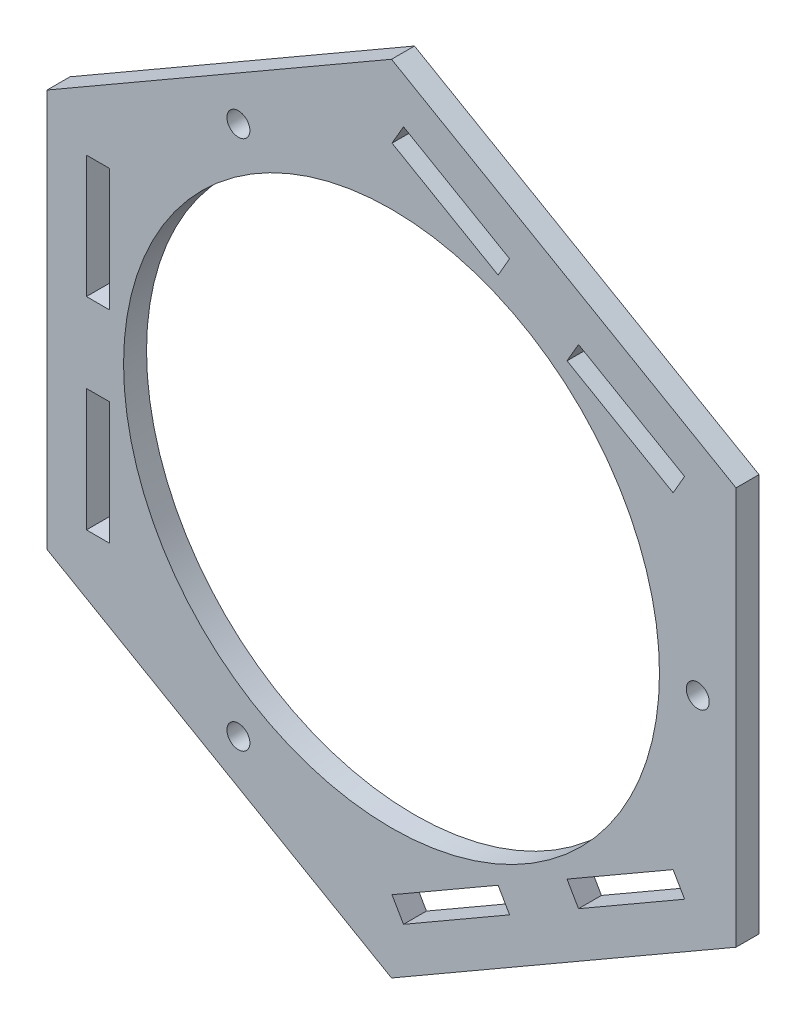
SolidWorks part; units mm, degrees
material "PMMA"
ref_plane "Спереди" through (0, 0, 0) normal (0, 0, 1) x (1, 0, 0)
ref_plane "Сверху" through (0, 0, 0) normal (0, 1, 0) x (1, 0, 0)
ref_plane "Справа" through (0, 0, 0) normal (1, 0, 0) x (0, 0, -1)
sketch "Эскиз2" plane through (0, 0, 0) normal (0, 0, 1) x (1, 0, 0)
  line L1 (0, 51.9615) -> (-45, 25.9808)
  line L2 (-45, 25.9808) -> (-45, -25.9808)
  line L3 (-45, -25.9808) -> (0, -51.9615)
  line L4 (0, -51.9615) -> (45, -25.9808)
  line L5 (45, -25.9808) -> (45, 25.9808)
  line L6 (45, 25.9808) -> (0, 51.9615)
  circle A0 centre (0, 0) radius 45 construction
  circle A1 centre (0, 0) radius 35
  dimension "D1" = 90
  dimension "D2" = 70
sketch "Эскиз1" plane through (0, 0, 0) normal (0, 0, 1) x (1, 0, 0)
  line L0 (0, 0) -> (-39.846, 0) construction
  line L7 (-39.846, 0) -> (-39.846, -13.1973) construction
  line L8 (-39.846, -13.1973) -> (-36.8459, -13.1973)
  line L9 (-36.8459, -13.1973) -> (-36.8459, -5.1973)
  line L10 (-36.8459, -5.1973) -> (-39.846, -5.1973)
  line L11 (-39.846, -5.1973) -> (-39.846, -13.1973)
  line L12 (-39.846, -13.1973) -> (-39.846, -21.1973)
  line L13 (-39.846, -21.1973) -> (-36.8459, -21.1973)
  line L14 (-36.8459, -21.1973) -> (-36.8459, -13.1973)
  dimension "D1" = 8
  dimension "D2" = 39.846
  dimension "D3" = 13.1973
  dimension "D4" = 16
extrude "Бобышка-Вытянуть1" add sketch "Эскиз2" along normal blind 3
extrude "Вырез-Вытянуть1" cut sketch "Эскиз1" along normal blind 3 contours L13 L14 L8 L12 | L10 L11 L8 L9
mirror "Зеркальное отражение1" about plane through (0, 0, 0) normal (0, 1, 0) of "Вырез-Вытянуть1"
pattern_circular "Круговой массив1" count 3 over 360 about axis through (0, 0, 0) along (0, 0, 1) of "Зеркальное отражение1", "Вырез-Вытянуть1"
sketch "Эскиз3" plane through (0, 0, 0) normal (0, 0, 1) x (1, 0, 0)
  circle A0 centre (0, 0) radius 40 construction
  circle A1 centre (40, 0) radius 1.5
  circle A2 centre (-20, -34.641) radius 1.5
  circle A3 centre (-20, 34.641) radius 1.5
  point P12 (0, 0)
  dimension "D1" = 3
extrude "Вырез-Вытянуть3" cut sketch "Эскиз3" along normal blind 10
